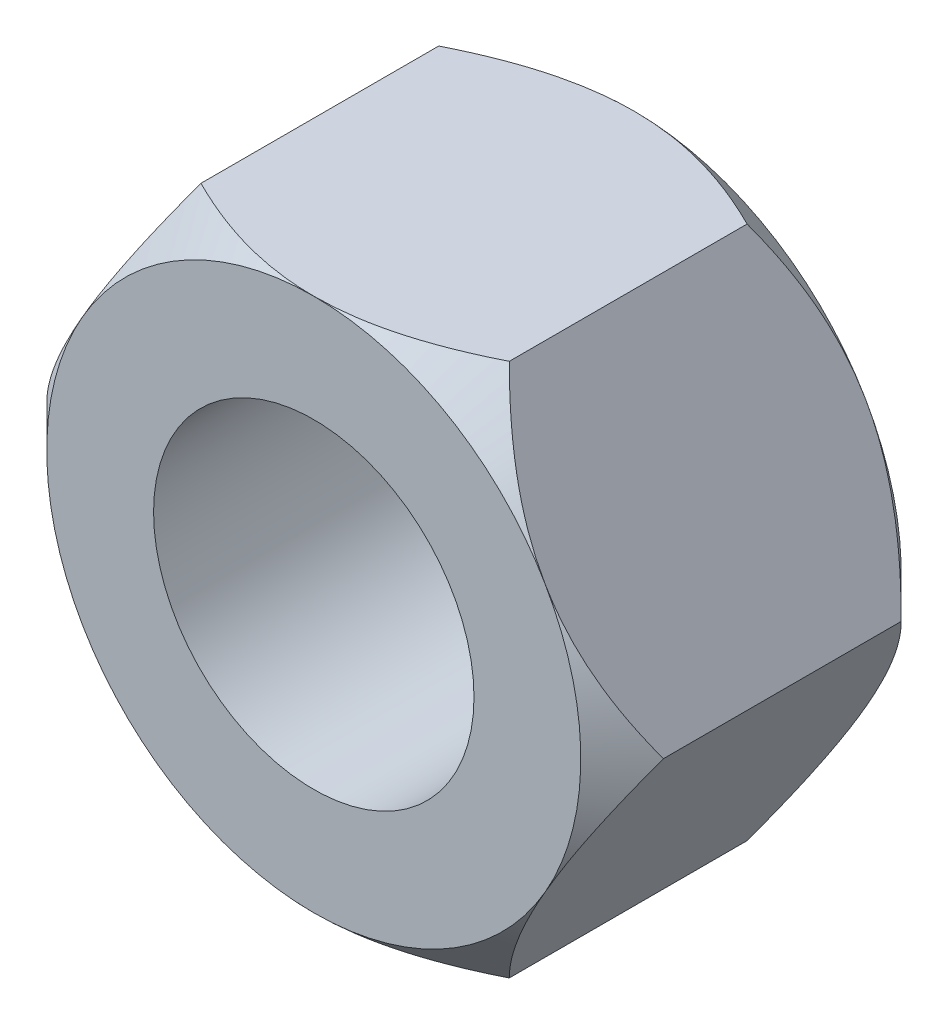
SolidWorks part; units mm, degrees
ref_plane "Front Plane" through (0, 0, 0) normal (0, 0, 1) x (1, 0, 0)
ref_plane "Top Plane" through (0, 0, 0) normal (0, 1, 0) x (1, 0, 0)
ref_plane "Right Plane" through (0, 0, 0) normal (1, 0, 0) x (0, 0, -1)
sketch "Sketch1" plane through (0, 0, 0) normal (0, 0, 1) x (1, 0, 0)
  line L1 (-4.3301, 7.5) -> (-8.6603, 0)
  line L2 (-8.6603, 0) -> (-4.3301, -7.5)
  line L3 (-4.3301, -7.5) -> (4.3301, -7.5)
  line L4 (4.3301, -7.5) -> (8.6603, 0)
  line L5 (8.6603, 0) -> (4.3301, 7.5)
  line L6 (4.3301, 7.5) -> (-4.3301, 7.5)
  circle A0 centre (0, 0) radius 7.5 construction
  circle A1 centre (0, 0) radius 4.5
  dimension "D1" = 9
  dimension "D2" = 15
extrude "Boss-Extrude2" add sketch "Sketch1" along normal mid plane 9
sketch "Sketch4" plane through (0, 0, 4.5) normal (0, 0, 1) x (1, 0, 0)
  circle A0 centre (0, 0) radius 7.5
extrude "Cut-Extrude2" cut sketch "Sketch4" against normal blind 9 draft 45 flip side to cut
mirror "Mirror3" about plane through (0, 0, 0) normal (0, 0, 1) of "Cut-Extrude2"
